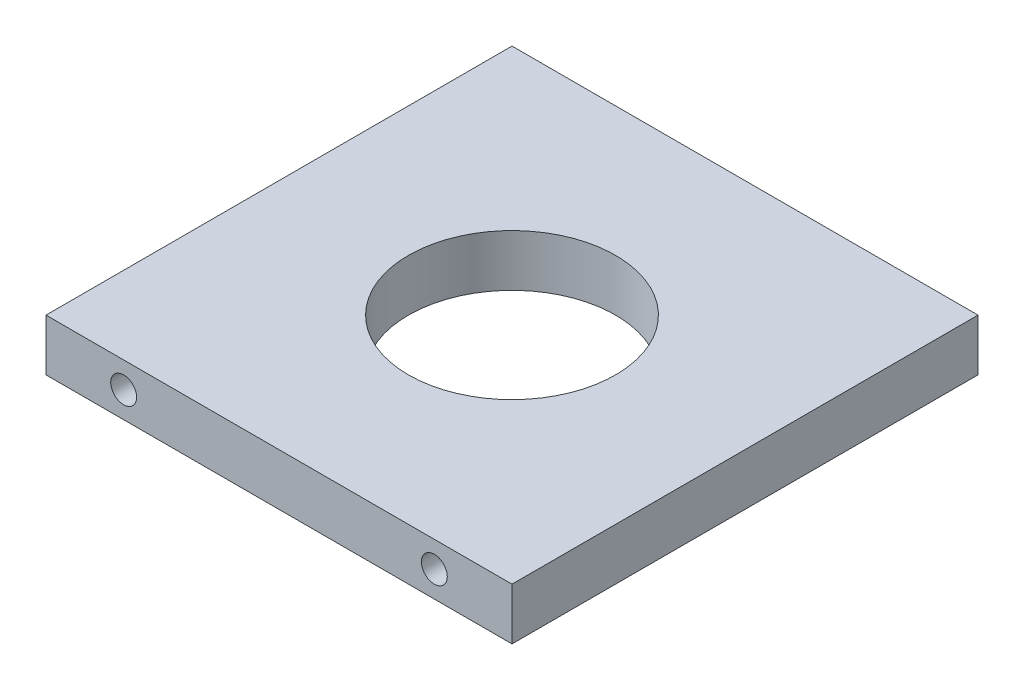
SolidWorks part; units mm, degrees
ref_plane "Front Plane" through (0, 0, 0) normal (0, 0, 1) x (1, 0, 0)
ref_plane "Top Plane" through (0, 0, 0) normal (0, 1, 0) x (1, 0, 0)
ref_plane "Right Plane" through (0, 0, 0) normal (1, 0, 0) x (0, 0, -1)
sketch "Sketch1" plane through (0, 0, 0) normal (0, 1, 0) x (1, 0, 0)
  line L1 (28.575, -28.575) -> (-28.575, -28.575)
  line L2 (28.575, -28.575) -> (28.575, 28.575)
  line L3 (28.575, 28.575) -> (-28.575, 28.575)
  line L4 (-28.575, -28.575) -> (-28.575, 28.575)
  line L5 (28.575, -28.575) -> (-28.575, 28.575) construction
  line L6 (28.575, 28.575) -> (-28.575, -28.575) construction
  circle A0 centre (0, 0) radius 12.7
  point P0 (0, 0)
  dimension "D2" = 25.4
  dimension "D1" = 57.15
extrude "Boss-Extrude1" add sketch "Sketch1" along normal blind 6.35 contours L4 L3 L2 L1
sketch "Sketch2" plane through (0, 0, 28.575) normal (0, 0, 1) x (1, 0, 0)
  line L0 (0, 0) -> (0, 6.35) construction
  line L3 (-28.575, 0) -> (28.575, 0) construction
  line L4 (-28.575, 6.35) -> (28.575, 6.35) construction
  line L5 (-19.05, 3.175) -> (19.05, 3.175) construction
  circle A0 centre (-19.05, 3.175) radius 1.5875
  circle A1 centre (19.05, 3.175) radius 1.5875
  point P10 (0, 3.175)
  dimension "D2" = 3.175
  dimension "D1" = 38.1
extrude "Cut-Extrude1" cut sketch "Sketch2" against normal blind 12.7
